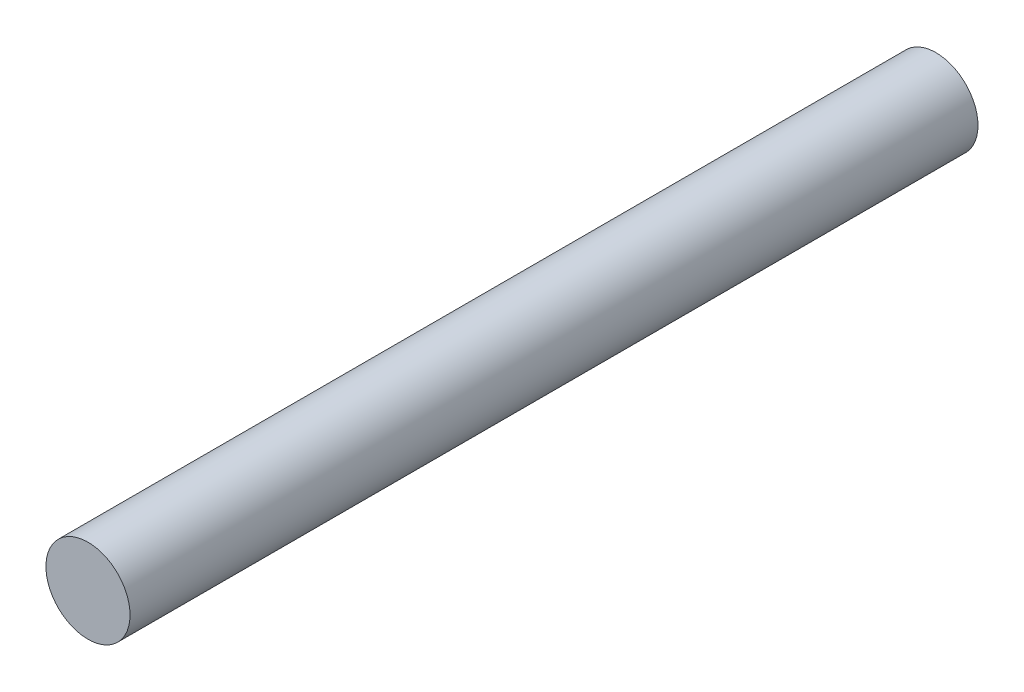
SolidWorks part; units mm, degrees
ref_plane "Front Plane" through (0, 0, 0) normal (0, 0, 1) x (1, 0, 0)
ref_plane "Top Plane" through (0, 0, 0) normal (0, 1, 0) x (1, 0, 0)
ref_plane "Right Plane" through (0, 0, 0) normal (1, 0, 0) x (0, 0, -1)
sketch "Sketch1" plane through (0, 0, 0) normal (0, 0, 1) x (1, 0, 0)
  circle A0 centre (0, 0) radius 6.2
  dimension "D1" = 12.4
extrude "Boss-Extrude1" add sketch "Sketch1" along normal blind 125
